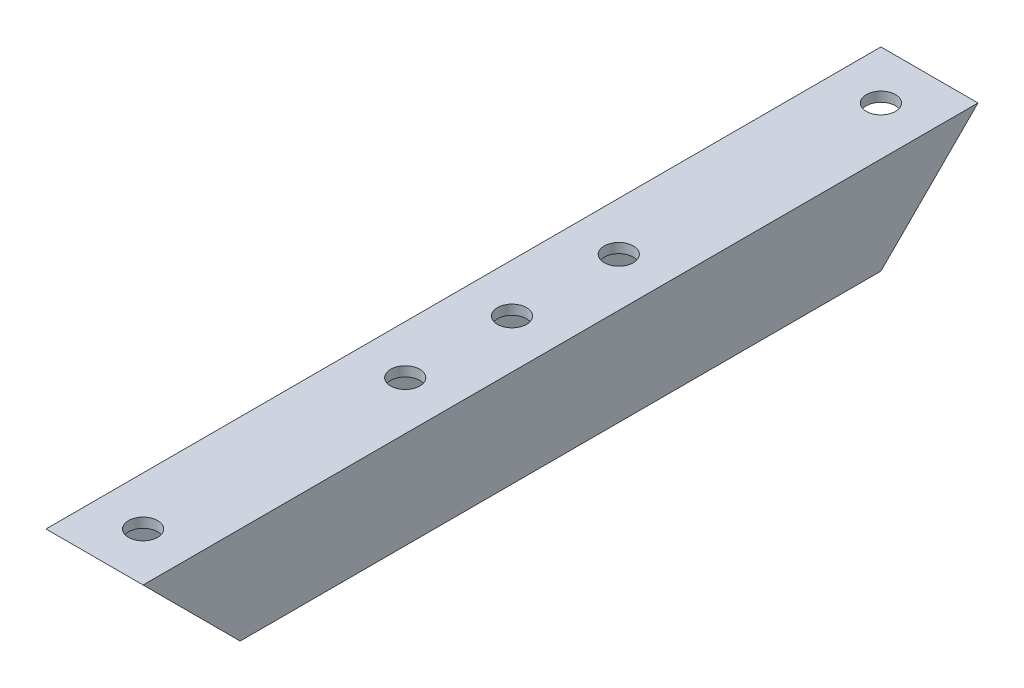
SolidWorks part; units mm, degrees
material "6063-O"
ref_plane "前视基准面" through (0, 0, 0) normal (0, 0, 1) x (1, 0, 0)
ref_plane "上视基准面" through (0, 0, 0) normal (0, 1, 0) x (1, 0, 0)
ref_plane "右视基准面" through (0, 0, 0) normal (1, 0, 0) x (0, 0, -1)
other "Configuration Table"
sketch "草图1" plane through (0, 0, 0) normal (0, 0, 1) x (1, 0, 0)
  line L1 (-5, 5) -> (5, 5)
  line L2 (-5, 5) -> (-5, -5)
  line L3 (-5, -5) -> (5, -5)
  line L4 (5, 5) -> (5, -5)
  line L5 (-5, 5) -> (5, -5) construction
  line L6 (-5, -5) -> (5, 5) construction
  point P4 (0, 0)
  dimension "D1" = 10
  dimension "D2" = 10
extrude "拉伸-薄壁1" add sketch "草图1" along normal blind 86 thin
sketch "草图2" plane through (0, 5, 0) normal (0, 1, 0) x (1, 0, 0)
  line L0 (0, -86) -> (0, 0) construction
  line L1 (5, -86) -> (-5, -86) construction
  line L2 (5, 0) -> (-5, 0) construction
  line L3 (0, -43) -> (5, -43) construction
  line L4 (5, -86) -> (5, 0) construction
  circle A0 centre (0, -54) radius 1.5
  circle A1 centre (0, -32) radius 1.5
  circle A2 centre (0, -43) radius 1.5
  circle A3 centre (0, -81) radius 1.5
  circle A4 centre (0, -5) radius 1.5
  dimension "D1" = 3
  dimension "D2" = 22
  dimension "D3" = 5
extrude "切除-拉伸1" cut sketch "草图2" against normal through all
sketch "草图3" plane through (5, 0, 0) normal (1, 0, 0) x (0, 0, -1)
  line L0 (-86, 5) -> (-76, -5)
  line L1 (-86, -5) -> (-86, 5) construction
  line L2 (-86, -5) -> (0, -5) construction
  line L3 (-76, -5) -> (-86, -5)
  line L4 (-86, -5) -> (-86, 5)
  line L5 (-86, 5) -> (0, 5) construction
  line L6 (0, 5) -> (-10, -5)
  line L7 (-10, -5) -> (0, -5)
  line L8 (0, -5) -> (0, 5)
  line L9 (-43, 5) -> (-43, -5) construction
  dimension "D1" = 45
extrude "切除-拉伸2" cut sketch "草图3" against normal blind 10 contours L0 L3 L4
